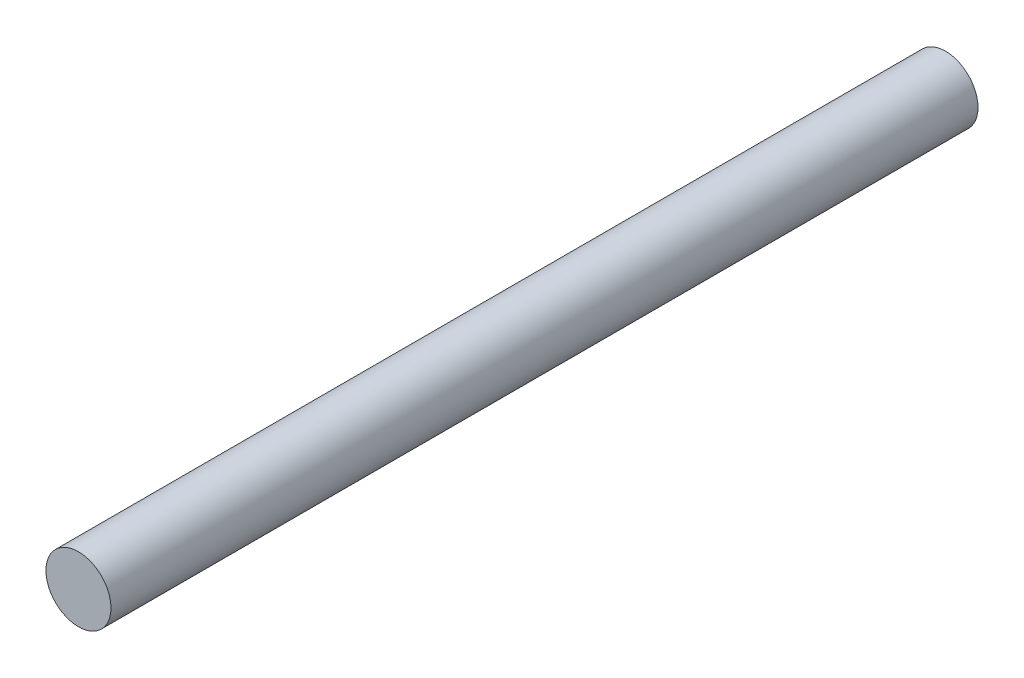
SolidWorks part; units mm, degrees
ref_plane "정면" through (0, 0, 0) normal (0, 0, 1) x (1, 0, 0)
ref_plane "윗면" through (0, 0, 0) normal (0, 1, 0) x (1, 0, 0)
ref_plane "우측면" through (0, 0, 0) normal (1, 0, 0) x (0, 0, -1)
sketch "스케치1" plane through (0, 0, 0) normal (0, 0, 1) x (1, 0, 0)
  circle A0 centre (0, 0) radius 1.5
  dimension "D1" = 3
extrude "보스-돌출1" add sketch "스케치1" along normal blind 40
